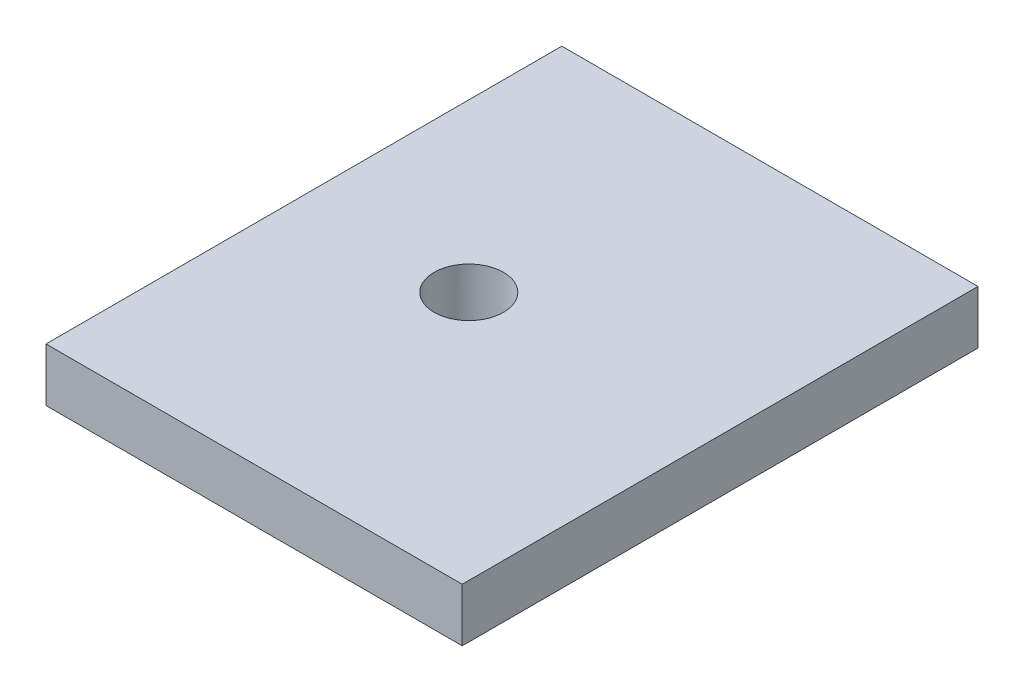
SolidWorks part; units mm, degrees
material "Custom Plastic"
ref_plane "Front Plane" through (0, 0, 0) normal (0, 0, 1) x (1, 0, 0)
ref_plane "Top Plane" through (0, 0, 0) normal (0, 1, 0) x (1, 0, 0)
ref_plane "Right Plane" through (0, 0, 0) normal (1, 0, 0) x (0, 0, -1)
sketch "Sketch1" plane through (0, 0, 0) normal (0, 1, 0) x (1, 0, 0)
  line L0 (-30.4611, 0) -> (33.997, 0) construction
  line L1 (-11.7, -14.5) -> (11.7, -14.5)
  line L2 (-11.7, -14.5) -> (-11.7, 14.5)
  line L3 (-11.7, 14.5) -> (11.7, 14.5)
  line L4 (11.7, -14.5) -> (11.7, 14.5)
  line L5 (-11.7, -14.5) -> (11.7, 14.5) construction
  line L6 (-11.7, 14.5) -> (11.7, -14.5) construction
  circle A0 centre (9, 8.9) radius 1
  circle A2 centre (9, -8.5) radius 1
  circle A3 centre (-9, -8.5) radius 1
  circle A5 centre (1.7, -8.5) radius 1
  spline S1 degree 3 poles (19.181, -14.2425) (19.8008, -12.3411) (17.8993, -11.7212) (17.2795, -13.6227) (16.6596, -15.5241) (18.5612, -16.144) (19.181, -14.2425) (19.8008, -12.3411) (17.8993, -11.7212) knots -0.5 0 0 0 0.5 0.5 0.5 1 1 1 1.5 1.5 1.5 weights 1 0.333333 0.333333 1 0.333333 0.333333 1 0.333333 0.333333 only from (19.181, -14.2425) to (19.181, -14.2425) construction
  spline S2 degree 3 poles (22.4885, -4.0962) (23.1083, -2.1947) (21.2068, -1.5749) (20.587, -3.4763) (19.9671, -5.3778) (21.8687, -5.9977) (22.4885, -4.0962) (23.1083, -2.1947) (21.2068, -1.5749) knots -0.5 0 0 0 0.5 0.5 0.5 1 1 1 1.5 1.5 1.5 weights 1 0.333333 0.333333 1 0.333333 0.333333 1 0.333333 0.333333 only from (22.4885, -4.0962) to (22.4885, -4.0962) construction
  spline S3 degree 3 poles (19.181, -14.2425) (19.8008, -12.3411) (17.8993, -11.7212) (17.2795, -13.6227) (16.6596, -15.5241) (18.5612, -16.144) (19.181, -14.2425) (19.8008, -12.3411) (17.8993, -11.7212) knots -0.5 0 0 0 0.5 0.5 0.5 1 1 1 1.5 1.5 1.5 weights 1 0.333333 0.333333 1 0.333333 0.333333 1 0.333333 0.333333 only from (19.181, -14.2425) to (19.181, -14.2425)
  spline S4 degree 3 poles (22.4885, -4.0962) (23.1083, -2.1947) (21.2068, -1.5749) (20.587, -3.4763) (19.9671, -5.3778) (21.8687, -5.9977) (22.4885, -4.0962) (23.1083, -2.1947) (21.2068, -1.5749) knots -0.5 0 0 0 0.5 0.5 0.5 1 1 1 1.5 1.5 1.5 weights 1 0.333333 0.333333 1 0.333333 0.333333 1 0.333333 0.333333 only from (22.4885, -4.0962) to (22.4885, -4.0962)
  point P0 (0, 0)
  point P6 (-9, 8.5)
  point P7 (9, 8.5)
  point P8 (9, 8.9)
  point P18 (1.7, 8.5)
  dimension "D7" = 17.4
  dimension "D8" = 18
  dimension "D10" = 2
  dimension "D1" = 29
  dimension "D2" = 23.4
  dimension "D3" = 6
  dimension "D4" = 6
  dimension "D5" = 18
  dimension "D6" = 2.7
  dimension "D9" = 10.7
extrude "Boss-Extrude1" add sketch "Sketch1" along normal blind 3
sketch "Sketch5" plane through (0, 0, 0) normal (0, -1, 0) x (1, 0, 0)
  circle A0 centre (-2.1456, 3.6104) radius 2.5 construction
  circle A1 centre (-2.1456, 3.6104) radius 2.5 construction
  circle A2 centre (-2.1456, 3.6104) radius 1.44
  dimension "D1" = 2.88
extrude "Cut-Extrude3" cut sketch "Sketch5" against normal blind 10
sketch "Sketch7" plane through (0, 3, 0) normal (0, 1, 0) x (1, 0, 0)
  spline S0 degree 3 poles (19.181, -14.2425) (19.8008, -12.3411) (17.8993, -11.7212) (17.2795, -13.6227) (16.6596, -15.5241) (18.5612, -16.144) (19.181, -14.2425) (19.8008, -12.3411) (17.8993, -11.7212) knots -0.5 0 0 0 0.5 0.5 0.5 1 1 1 1.5 1.5 1.5 weights 1 0.333333 0.333333 1 0.333333 0.333333 1 0.333333 0.333333 only from (19.181, -14.2425) to (19.181, -14.2425) construction
  spline S1 degree 3 poles (22.4885, -4.0962) (23.1083, -2.1947) (21.2068, -1.5749) (20.587, -3.4763) (19.9671, -5.3778) (21.8687, -5.9977) (22.4885, -4.0962) (23.1083, -2.1947) (21.2068, -1.5749) knots -0.5 0 0 0 0.5 0.5 0.5 1 1 1 1.5 1.5 1.5 weights 1 0.333333 0.333333 1 0.333333 0.333333 1 0.333333 0.333333 only from (22.4885, -4.0962) to (22.4885, -4.0962) construction
  spline S2 degree 3 poles (19.181, -14.2425) (19.8008, -12.3411) (17.8993, -11.7212) (17.2795, -13.6227) (16.6596, -15.5241) (18.5612, -16.144) (19.181, -14.2425) (19.8008, -12.3411) (17.8993, -11.7212) knots -0.5 0 0 0 0.5 0.5 0.5 1 1 1 1.5 1.5 1.5 weights 1 0.333333 0.333333 1 0.333333 0.333333 1 0.333333 0.333333 only from (19.181, -14.2425) to (19.181, -14.2425)
  spline S3 degree 3 poles (22.4885, -4.0962) (23.1083, -2.1947) (21.2068, -1.5749) (20.587, -3.4763) (19.9671, -5.3778) (21.8687, -5.9977) (22.4885, -4.0962) (23.1083, -2.1947) (21.2068, -1.5749) knots -0.5 0 0 0 0.5 0.5 0.5 1 1 1 1.5 1.5 1.5 weights 1 0.333333 0.333333 1 0.333333 0.333333 1 0.333333 0.333333 only from (22.4885, -4.0962) to (22.4885, -4.0962)
extrude "Cut-Extrude4" cut sketch "Sketch7" against normal blind 10
sketch "Sketch8" plane through (0, 3, 0) normal (0, 1, 0) x (1, 0, 0)
  line L0 (24.633, 0) -> (-21.7502, 0) construction
  line L1 (1.7, -8.5) -> (1.7, 20.7764) construction
  line L2 (-9, -8.5) -> (-9, 21.3011) construction
  line L3 (9, -8.5) -> (9, 8.9) construction
  line L4 (14.3582, 8.9) -> (-23.7207, 8.9) construction
  circle A0 centre (1.7, 8.9) radius 1
  circle A1 centre (-9, 8.9) radius 1
  point P15 (1.7, 8.9)
  point P16 (-9, 8.9)
  dimension "D1" = 2
  dimension "D2" = 2
extrude "Cut-Extrude5" cut sketch "Sketch8" against normal blind 10
sketch "Sketch9" plane through (0, 3, 0) normal (0, 1, 0) x (1, 0, 0)
  circle A0 centre (-2.1456, -3.6104) radius 3.027
extrude "Boss-Extrude3" add sketch "Sketch9" against normal up to surface (3 mm away) up to face at (-9, 0, -9.9)
sketch "Sketch10" plane through (0, 3, 0) normal (0, 1, 0) x (1, 0, 0)
  line L0 (-11.7, -14.5) -> (11.7, -14.5) construction
  line L1 (-11.7, 14.5) -> (-11.7, -14.5) construction
  circle A1 centre (-2.3282, -0.1) radius 1.5 construction
  circle A2 centre (-2.3282, -0.1) radius 1.95
  dimension "D1" = 3.9
  dimension "D2" = 14.4
  dimension "D3" = 9.3718
extrude "Cut-Extrude6" cut sketch "Sketch10" against normal blind 10
sketch "Sketch11" plane through (0, 3, 0) normal (0, 1, 0) x (1, 0, 0)
  line L4 (11.7, -14.5) -> (11.7, 14.5)
  line L5 (11.7, 14.5) -> (-11.7, 14.5)
  line L6 (-11.7, 14.5) -> (-11.7, -14.5)
  line L7 (-11.7, -14.5) -> (11.7, -14.5)
  line L8 (11.7, -14.5) -> (11.7, 14.5)
  line L9 (11.7, 14.5) -> (-11.7, 14.5)
  line L10 (-11.7, 14.5) -> (-11.7, -14.5)
  line L11 (-11.7, -14.5) -> (11.7, -14.5)
  circle A0 centre (-2.3282, -0.1) radius 1.95 construction
  circle A1 centre (-2.3282, -0.1) radius 1.95
  dimension "D1" = 0
extrude "Boss-Extrude4" add sketch "Sketch11" against normal up to surface (3 mm away) up to face at (-2.3282, 0, -1.85)
